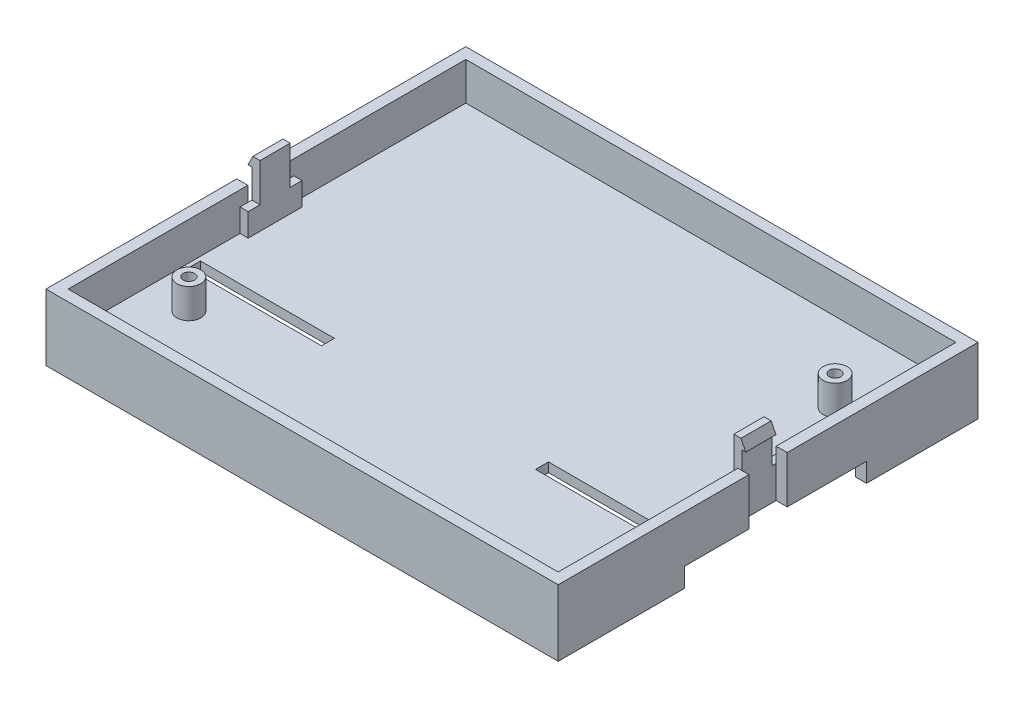
SolidWorks part; units mm, degrees
ref_plane "Alzado" through (0, 0, 0) normal (0, 0, 1) x (1, 0, 0)
ref_plane "Planta" through (0, 0, 0) normal (0, 1, 0) x (1, 0, 0)
ref_plane "Vista lateral" through (0, 0, 0) normal (1, 0, 0) x (0, 0, -1)
ref_plane "Plano1" through (0, 18.75, 0) normal (0, 1, 0) x (1, 0, 0)
sketch "Croquis1" plane through (0, 18.75, 0) normal (0, 1, 0) x (1, 0, 0)
  line L0 (-51.99, 3.15) -> (51.99, 3.15)
  line L1 (51.99, 3.15) -> (51.99, 5.625)
  line L2 (51.99, 5.625) -> (-51.99, 5.625)
  line L3 (-51.99, 5.625) -> (-51.99, 3.15)
extrude "Saliente-Extruir1" add sketch "Croquis1" against normal blind 2
sketch "Croquis2" plane through (0, 0, -3.15) normal (0, 0, 1) x (1, 0, 0)
  line L0 (-51.99, 16.75) -> (-50.99, 18.75)
  line L1 (-50.99, 18.75) -> (50.99, 18.75)
  line L2 (50.99, 18.75) -> (51.99, 16.75)
  line L3 (51.99, 16.75) -> (-51.99, 16.75)
extrude "Saliente-Extruir2" add sketch "Croquis2" along normal blind 6.3
sketch "Croquis3" plane through (0, 16.75, 0) normal (0, -1, 0) x (1, 0, 0)
  line L0 (51.99, -5.625) -> (-51.99, -5.625)
  line L1 (-51.99, -5.625) -> (-51.99, 3.15)
  line L2 (-51.99, 3.15) -> (51.99, 3.15)
  line L3 (51.99, 3.15) -> (51.99, -5.625)
extrude "Saliente-Extruir3" add sketch "Croquis3" along normal blind 12.75
sketch "Croquis4" plane through (51.99, 0, 0) normal (1, 0, 0) x (0, 0, -1)
  line L0 (5.625, 4) -> (5.625, 18.75)
  line L1 (5.625, 18.75) -> (3.15, 18.75)
  line L2 (3.15, 18.75) -> (3.15, 18.35)
  line L3 (3.15, 18.35) -> (3.15, 16.75)
  line L4 (3.15, 16.75) -> (-3.15, 16.75)
  line L5 (-3.15, 16.75) -> (-3.15, 4)
  line L6 (-3.15, 4) -> (5.625, 4)
extrude "Cortar-Extruir1" cut sketch "Croquis4" against normal blind 0.8
sketch "Croquis5" plane through (-51.99, 0, 0) normal (-1, 0, 0) x (0, 0, 1)
  line L0 (-5.625, 4) -> (3.15, 4)
  line L1 (3.15, 4) -> (3.15, 16.75)
  line L2 (3.15, 16.75) -> (-3.15, 16.75)
  line L3 (-3.15, 16.75) -> (-3.15, 18.35)
  line L4 (-3.15, 18.35) -> (-3.15, 18.75)
  line L5 (-3.15, 18.75) -> (-5.625, 18.75)
  line L6 (-5.625, 18.75) -> (-5.625, 4)
extrude "Cortar-Extruir2" cut sketch "Croquis5" against normal blind 0.8
ref_plane "Plano2" through (49.49, 0, 0) normal (1, 0, 0) x (0, 0, -1)
sketch "Croquis6" plane through (49.49, 0, 0) normal (1, 0, 0) x (0, 0, -1)
  line L0 (-3.15, 18.75) -> (-3.15, 5.95)
  line L1 (-3.15, 5.95) -> (5.625, 5.95)
  line L2 (5.625, 5.95) -> (5.625, 18.75)
  line L3 (5.625, 18.75) -> (-3.15, 18.75)
extrude "Cortar-Extruir3" cut sketch "Croquis6" against normal blind 98.98
sketch "Croquis7" plane through (0, 18.75, 0) normal (0, 1, 0) x (-1, 0, 0)
  line L0 (49.49, -3.15) -> (49.49, -5.625)
  line L1 (49.49, -5.625) -> (51.19, -5.625)
  line L2 (51.19, -5.625) -> (51.19, -3.15)
  line L3 (51.19, -3.15) -> (49.49, -3.15)
  line L4 (-51.19, -3.15) -> (-51.19, -5.625)
  line L5 (-51.19, -5.625) -> (-49.49, -5.625)
  line L6 (-49.49, -5.625) -> (-49.49, -3.15)
  line L7 (-49.49, -3.15) -> (-51.19, -3.15)
extrude "Cortar-Extruir4" cut sketch "Croquis7" against normal blind 2
sketch "Croquis8" plane through (0, 16.75, 0) normal (0, 1, 0) x (-1, 0, 0)
  line L0 (-51.19, -3.15) -> (-51.19, -5.625)
  line L1 (-51.19, -5.625) -> (-49.49, -5.625)
  line L2 (-49.49, -5.625) -> (-49.49, -3.15)
  line L3 (-49.49, -3.15) -> (-51.19, -3.15)
extrude "Cortar-Extruir5" cut sketch "Croquis8" against normal blind 6
sketch "Croquis9" plane through (0, 16.75, 0) normal (0, 1, 0) x (-1, 0, 0)
  line L0 (49.49, -3.15) -> (49.49, -5.625)
  line L1 (49.49, -5.625) -> (51.19, -5.625)
  line L2 (51.19, -5.625) -> (51.19, -3.15)
  line L3 (51.19, -3.15) -> (49.49, -3.15)
extrude "Cortar-Extruir6" cut sketch "Croquis9" against normal blind 6
sketch "Croquis10" plane through (0, 0, 3.15) normal (0, 0, 1) x (1, 0, 0)
  line L0 (49.49, 5.95) -> (49.49, 10.75)
  line L1 (49.49, 10.75) -> (51.19, 10.75)
  line L2 (51.19, 10.75) -> (51.19, 4)
  line L3 (51.19, 4) -> (-51.19, 4)
  line L4 (-51.19, 4) -> (-51.19, 10.75)
  line L5 (-51.19, 10.75) -> (-49.49, 10.75)
  line L6 (-49.49, 10.75) -> (-49.49, 5.95)
  line L7 (-49.49, 5.95) -> (49.49, 5.95)
extrude "Saliente-Extruir4" add sketch "Croquis10" along normal blind 2.475
sketch "Croquis11" plane through (0, 0, 5.625) normal (0, 0, 1) x (1, 0, 0)
  line L0 (51.19, 5.95) -> (51.19, 4)
  line L1 (51.19, 4) -> (-51.19, 4)
  line L2 (-51.19, 4) -> (-51.19, 5.95)
  line L3 (-51.19, 5.95) -> (51.19, 5.95)
extrude "Saliente-Extruir5" add sketch "Croquis11" along normal blind 38.225
sketch "Croquis12" plane through (0, 5.95, 0) normal (0, 1, 0) x (-1, 0, 0)
  line L0 (51.19, 41.54) -> (-51.19, 41.54)
  line L1 (-51.19, 41.54) -> (-51.19, 43.85)
  line L2 (-51.19, 43.85) -> (51.19, 43.85)
  line L3 (51.19, 43.85) -> (51.19, 41.54)
extrude "Saliente-Extruir6" add sketch "Croquis12" along normal blind 7.9
sketch "Croquis13" plane through (0, 0, -5.625) normal (0, 0, -1) x (-1, 0, 0)
  line L0 (51.19, 5.95) -> (51.19, 4)
  line L1 (51.19, 4) -> (-51.19, 4)
  line L2 (-51.19, 4) -> (-51.19, 5.95)
  line L3 (-51.19, 5.95) -> (51.19, 5.95)
extrude "Saliente-Extruir7" add sketch "Croquis13" along normal blind 38.225
sketch "Croquis14" plane through (-51.19, 0, 0) normal (-1, 0, 0) x (0, 0, 1)
  line L0 (43.85, 4) -> (4, 4)
  line L1 (4, 4) -> (4, 13.85)
  line L2 (4, 13.85) -> (43.85, 13.85)
  line L3 (43.85, 13.85) -> (43.85, 4)
extrude "Saliente-Extruir8" add sketch "Croquis14" along normal blind 2.31
sketch "Croquis15" plane through (51.19, 0, 0) normal (1, 0, 0) x (0, 0, -1)
  line L0 (-43.85, 4) -> (-43.85, 13.85)
  line L1 (-43.85, 13.85) -> (-4, 13.85)
  line L2 (-4, 13.85) -> (-4, 4)
  line L3 (-4, 4) -> (-43.85, 4)
extrude "Saliente-Extruir9" add sketch "Croquis15" along normal blind 2.31
sketch "Croquis16" plane through (0, 5.95, 0) normal (0, 1, 0) x (-1, 0, 0)
  line L0 (22.36, 14.74) -> (50.36, 14.74)
  line L1 (50.36, 14.74) -> (50.36, 17.44)
  line L2 (50.36, 17.44) -> (22.36, 17.44)
  line L3 (22.36, 17.44) -> (22.36, 14.74)
extrude "Cortar-Extruir7" cut sketch "Croquis16" against normal through all
sketch "Croquis17" plane through (0, 5.95, 0) normal (0, 1, 0) x (-1, 0, 0)
  line L0 (-22.36, 14.74) -> (-22.36, 17.44)
  line L1 (-22.36, 17.44) -> (-50.36, 17.44)
  line L2 (-50.36, 17.44) -> (-50.36, 14.74)
  line L3 (-50.36, 14.74) -> (-22.36, 14.74)
extrude "Cortar-Extruir8" cut sketch "Croquis17" against normal through all
sketch "Croquis18" plane through (0, 4, 0) normal (0, -1, 0) x (1, 0, 0)
  line L0 (53.5, 17.44) -> (-53.5, 17.44)
  line L1 (-53.5, 17.44) -> (-53.5, 43.85)
  line L2 (-53.5, 43.85) -> (53.5, 43.85)
  line L3 (53.5, 43.85) -> (53.5, 17.44)
extrude "Saliente-Extruir10" add sketch "Croquis18" along normal blind 4
sketch "Croquis19" plane through (0, 5.95, 0) normal (0, 1, 0) x (-1, 0, 0)
  line L0 (-51.19, -41.54) -> (51.19, -41.54)
  line L1 (51.19, -41.54) -> (51.19, -43.85)
  line L2 (51.19, -43.85) -> (-51.19, -43.85)
  line L3 (-51.19, -43.85) -> (-51.19, -41.54)
extrude "Saliente-Extruir11" add sketch "Croquis19" along normal blind 7.9
sketch "Croquis20" plane through (51.19, 0, 0) normal (1, 0, 0) x (0, 0, -1)
  line L0 (43.85, 4) -> (4, 4)
  line L1 (4, 4) -> (4, 13.85)
  line L2 (4, 13.85) -> (43.85, 13.85)
  line L3 (43.85, 13.85) -> (43.85, 4)
extrude "Saliente-Extruir12" add sketch "Croquis20" along normal blind 2.31
sketch "Croquis21" plane through (-51.19, 0, 0) normal (-1, 0, 0) x (0, 0, 1)
  line L0 (-43.85, 4) -> (-43.85, 13.85)
  line L1 (-43.85, 13.85) -> (-4, 13.85)
  line L2 (-4, 13.85) -> (-4, 4)
  line L3 (-4, 4) -> (-43.85, 4)
extrude "Saliente-Extruir13" add sketch "Croquis21" along normal blind 2.31
sketch "Croquis22" plane through (0, 4, 0) normal (0, -1, 0) x (1, 0, 0)
  line L0 (-53.5, -43.85) -> (-53.5, -20.56)
  line L1 (-53.5, -20.56) -> (-51.19, -20.56)
  line L2 (-51.19, -20.56) -> (-51.19, -41.54)
  line L3 (-51.19, -41.54) -> (-10.19, -41.54)
  line L4 (-10.19, -41.54) -> (-10.19, -22.86)
  line L5 (-10.19, -22.86) -> (-40.69, -22.86)
  line L6 (-40.69, -22.86) -> (-42.7044, -23.54)
  line L7 (-42.7044, -23.54) -> (-43.44, -21.3608)
  line L8 (-43.44, -21.3608) -> (-41.0677, -20.56)
  line L9 (-41.0677, -20.56) -> (-6.19, -20.56)
  line L10 (-6.19, -20.56) -> (-6.19, -43.85)
  line L11 (-6.19, -43.85) -> (-53.5, -43.85)
extrude "Saliente-Extruir14" add sketch "Croquis22" along normal blind 4
sketch "Croquis23" plane through (0, 4, 0) normal (0, -1, 0) x (1, 0, 0)
  line L0 (53.5, -43.85) -> (6.19, -43.85)
  line L1 (6.19, -43.85) -> (6.19, -20.56)
  line L2 (6.19, -20.56) -> (41.0677, -20.56)
  line L3 (41.0677, -20.56) -> (43.44, -21.3608)
  line L4 (43.44, -21.3608) -> (42.7044, -23.54)
  line L5 (42.7044, -23.54) -> (40.69, -22.86)
  line L6 (40.69, -22.86) -> (10.19, -22.86)
  line L7 (10.19, -22.86) -> (10.19, -41.54)
  line L8 (10.19, -41.54) -> (51.19, -41.54)
  line L9 (51.19, -41.54) -> (51.19, -20.56)
  line L10 (51.19, -20.56) -> (53.5, -20.56)
  line L11 (53.5, -20.56) -> (53.5, -43.85)
extrude "Saliente-Extruir15" add sketch "Croquis23" along normal blind 4
sketch "Croquis24" plane through (0, 0, 17.44) normal (0, 0, -1) x (-1, 0, 0)
  line L0 (-23.5, 4) -> (-23.5, 0)
  line L1 (-23.5, 0) -> (23.5, 0)
  line L2 (23.5, 0) -> (23.5, 4)
  line L3 (23.5, 4) -> (-23.5, 4)
extrude "Cortar-Extruir9" cut sketch "Croquis24" against normal blind 24.1
ref_plane "Plano3" through (51.19, 0, 0) normal (1, 0, 0) x (0, 0, -1)
sketch "Croquis25" plane through (51.19, 0, 0) normal (1, 0, 0) x (0, 0, -1)
  line L0 (-41.54, 4) -> (-41.54, 0)
  line L1 (-41.54, 0) -> (-19.24, 0)
  line L2 (-19.24, 0) -> (-19.24, 4)
  line L3 (-19.24, 4) -> (-41.54, 4)
extrude "Cortar-Extruir10" cut sketch "Croquis25" against normal up to next
ref_plane "Plano4" through (-51.19, 0, 0) normal (-1, 0, 0) x (0, -1, 0)
sketch "Croquis26" plane through (-51.19, 0, 0) normal (-1, 0, 0) x (0, -1, 0)
  line L0 (-4, 19.24) -> (0, 19.24)
  line L1 (0, 19.24) -> (0, 41.54)
  line L2 (0, 41.54) -> (-4, 41.54)
  line L3 (-4, 41.54) -> (-4, 19.24)
extrude "Cortar-Extruir11" cut sketch "Croquis26" against normal up to next
ref_plane "Plano5" through (23.5, 0, 0) normal (-1, 0, 0) x (0, -1, 0)
sketch "Croquis27" plane through (23.5, 0, 0) normal (-1, 0, 0) x (0, -1, 0)
  line L0 (-2.45, 16.74) -> (-0.45, 14.74)
  line L1 (-0.45, 14.74) -> (0, 14.74)
  line L2 (0, 14.74) -> (0, 17.44)
  line L3 (0, 17.44) -> (-2.45, 17.44)
  line L4 (-2.45, 17.44) -> (-2.45, 16.74)
extrude "Saliente-Extruir16" add sketch "Croquis27" against normal blind 25.9
ref_plane "Plano6" through (-23.5, 0, 0) normal (1, 0, 0) x (0, 0, -1)
sketch "Croquis28" plane through (-23.5, 0, 0) normal (1, 0, 0) x (0, 0, -1)
  line L0 (-14.74, 0.45) -> (-16.74, 2.45)
  line L1 (-16.74, 2.45) -> (-17.44, 2.45)
  line L2 (-17.44, 2.45) -> (-17.44, 0)
  line L3 (-17.44, 0) -> (-14.74, 0)
  line L4 (-14.74, 0) -> (-14.74, 0.45)
extrude "Saliente-Extruir17" add sketch "Croquis28" against normal blind 25.9
ref_plane "Plano7" through (0, 0, 25) normal (0, 0, 1) x (1, 0, 0)
sketch "Croquis29" plane through (0, 0, 25) normal (0, 0, 1) x (1, 0, 0)
  line L0 (-40, 12.15) -> (-42.5, 12.15)
  line L1 (-42.5, 12.15) -> (-42.5, 5.95)
  line L2 (-42.5, 5.95) -> (-40, 5.95)
  line L3 (-40, 5.95) -> (-40, 12.15)
  line L4 (-42.5, 12.15) -> (-42.5, 5.95) construction
revolve "Revolución1" add sketch "Croquis29" angle 360 about L4
ref_plane "Plano8" through (0, 0, -25) normal (0, 0, 1) x (1, 0, 0)
sketch "Croquis30" plane through (0, 0, -25) normal (0, 0, 1) x (1, 0, 0)
  line L0 (45, 12.15) -> (42.5, 12.15)
  line L1 (42.5, 12.15) -> (42.5, 5.95)
  line L2 (42.5, 5.95) -> (45, 5.95)
  line L3 (45, 5.95) -> (45, 12.15)
  line L4 (42.5, 12.15) -> (42.5, 5.95) construction
revolve "Revolución2" add sketch "Croquis30" angle 360 about L4
hole_wizard "Diámetro de taladro Ø2.4 (2.4)1" positions "Croquis32" profile "Croquis31" hole size "Ø2.4" standard "Ansi Metric"
sketch "Croquis32" plane through (0, 12.15, 0) normal (0, 1, 0) x (1, 0, 0)
  point P0 (42.5, 25)
  point P1 (-42.5, -25)
sketch "Croquis31" plane through (42.5, 12.15, -25) normal (1, 0, 0) x (0, 0, 1)
  line L0 (0, 0) -> (0, 6.2)
  line L1 (0, 6.2) -> (1.2, 6.2)
  line L2 (1.2, 6.2) -> (1.2, 0)
  line L5 (1.2, 0) -> (0, 0)
  line L10 (0, 6.2) -> (-1.2, 6.2) construction
  line L11 (0, -6.35) -> (0, 107.95) construction
  dimension "Diámetro de taladro" = 2.4
  dimension "Profundidad de taladro" = 6.2
  dimension "Ángulo de perforador" = 180
